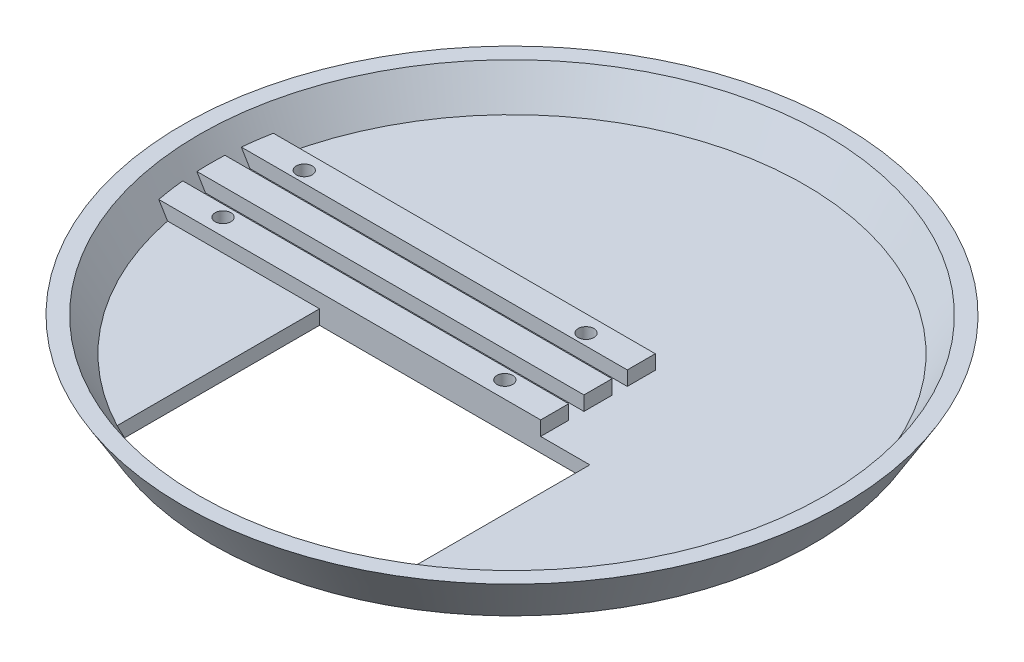
SolidWorks part; units mm, degrees
ref_plane "Front Plane" through (0, 0, 0) normal (0, 0, 1) x (1, 0, 0)
ref_plane "Top Plane" through (0, 0, 0) normal (0, 1, 0) x (1, 0, 0)
ref_plane "Right Plane" through (0, 0, 0) normal (1, 0, 0) x (0, 0, -1)
sketch "Sketch1" plane through (0, 0, 0) normal (0, 0, 1) x (1, 0, 0)
  line L0 (0, 0) -> (63, 0)
  line L1 (63, 0) -> (69, 10)
  line L6 (0, 3) -> (61.3014, 3)
  line L7 (61.3014, 3) -> (65.5014, 10)
  line L8 (69, 10) -> (65.5014, 10)
  line L9 (0, 0) -> (0, 3)
  line L10 (61.3014, 3) -> (66.4275, 11.5435) construction
  dimension "D1" = 69
  dimension "D2" = 63
  dimension "D3" = 10
  dimension "D4" = 3
revolve "Revolve1" add sketch "Sketch1" angle 360 about L9
sketch "Sketch2" plane through (0, 3, 0) normal (0, 1, 0) x (1, 0, 0)
  line L0 (-28.3, -12) -> (-28.3, -54.3781)
  line L1 (-28.3, -12) -> (28.3, -12)
  line L5 (28.3, -12) -> (28.3, -54.3781)
  arc A0 (-28.3, -54.3781) -> (28.3, -54.3781) centre (0, 0) ccw
  circle A3 centre (0, 0) radius 61.3014 construction
  dimension "D2" = 28.3
  dimension "D1" = 56.6
  dimension "D4" = 12
extrude "Cut-Extrude1" cut sketch "Sketch2" against normal through all
sketch "Sketch4" plane through (0, 0, 0) normal (1, 0, 0) x (0, 0, -1)
  line L0 (-6.1333, 3) -> (-12, 3)
  line L5 (-12, 3) -> (-12, 6)
  line L6 (-12, 6) -> (-6.1333, 6)
  line L7 (-6.1333, 6) -> (-6.1333, 3)
  line L8 (-2.9333, 3) -> (2.9333, 3)
  line L9 (2.9333, 3) -> (2.9333, 6)
  line L10 (2.9333, 6) -> (-2.9333, 6)
  line L11 (-2.9333, 6) -> (-2.9333, 3)
  line L12 (12, 3) -> (6.1333, 3)
  line L13 (6.1333, 3) -> (6.1333, 6)
  line L14 (6.1333, 6) -> (12, 6)
  line L15 (12, 6) -> (12, 3)
  point P13 (0, 3)
  dimension "D1" = 12
  dimension "D2" = 3
  dimension "D3" = 3
  dimension "D4" = 3.2
  dimension "D5" = 3.2
  dimension "D6" = 12
extrude "Boss-Extrude1" add sketch "Sketch4" along normal blind 10 and the other way blind 63.5
sketch "Sketch5" plane through (0, 0, 0) normal (0, 1, 0) x (1, 0, 0)
  line L0 (10, 2.9333) -> (10, -2.9333) construction
  circle A0 centre (7, -8.5) radius 1.65
  circle A1 centre (7, 0) radius 1.65
  circle A2 centre (7, 8.5) radius 1.65
  circle A6 centre (-52, 8.5) radius 1.65
  circle A8 centre (-52, -8.5) radius 1.65
  circle A9 centre (-22.5, 0) radius 1.65 [skipped]
  circle A10 centre (-52, 0) radius 1.65 [skipped]
  circle A11 centre (-22.5, 8.5) radius 1.65 [skipped]
  circle A12 centre (-22.5, -8.5) radius 1.65 [skipped]
  dimension "D2" = 3.3
  dimension "D3" = 8.5
  dimension "D6" = 3
  dimension "D7" = 59
  dimension "D4" = 8.5
  dimension "D5" = 3
extrude "Cut-Extrude2" cut sketch "Sketch5" along normal through all contours A2 | A0 | A8 | A6
sketch "Sketch7" [suppressed] plane through (10, 0, 0) normal (1, 0, 0) x (0, 0, -1)
  line L0 (-12, 37.9) -> (-6.1333, 37.9) construction
  line L1 (-12, 3) -> (-6.1333, 3)
  line L2 (-12, 3) -> (-12, 43)
  line L3 (-12, 43) -> (12, 43)
  line L4 (12, 3) -> (12, 43)
  line L5 (-2.9333, 37.9) -> (2.9333, 37.9) construction
  line L6 (-6.1333, 37.9) -> (-2.9333, 37.9)
  line L7 (-6.1333, 37.9) -> (-6.1333, 40.9)
  line L8 (-6.1333, 40.9) -> (-2.9333, 40.9)
  line L9 (-2.9333, 37.9) -> (-2.9333, 40.9)
  line L10 (12, 37.9) -> (6.1333, 37.9) construction
  line L11 (2.9333, 3) -> (2.9333, 6)
  line L12 (2.9333, 37.9) -> (6.1333, 37.9)
  line L13 (2.9333, 37.9) -> (2.9333, 40.9)
  line L14 (2.9333, 40.9) -> (6.1333, 40.9)
  line L15 (6.1333, 37.9) -> (6.1333, 40.9)
  line L20 (2.9333, 6) -> (6.1333, 6)
  line L21 (6.1333, 6) -> (6.1333, 3)
  line L22 (-6.1333, 3) -> (-6.1333, 6)
  line L23 (-6.1333, 6) -> (-2.9333, 6)
  line L24 (-2.9333, 6) -> (-2.9333, 3)
  line L25 (6.1333, 3) -> (12, 3)
  line L26 (-2.9333, 3) -> (2.9333, 3)
  circle A0 centre (0, 23.5) radius 8.5
  point P18 (0, 3)
  dimension "D6" = 17
  dimension "D7" = 20.5
  dimension "D1" = 24
  dimension "D2" = 40
  dimension "D3" = 3.2
  dimension "D4" = 3
  dimension "D5" = 37.9
sketch "Sketch8" plane through (10, 0, 0) normal (1, 0, 0) x (0, 0, -1)
  line L1 (-12, 6) -> (-6.1333, 6)
  line L2 (-12, 6) -> (-12, 3)
  line L3 (-12, 3) -> (-6.1333, 3)
  line L4 (-6.1333, 6) -> (-6.1333, 3)
  line L5 (-2.9333, 6) -> (2.9333, 6)
  line L6 (-2.9333, 6) -> (-2.9333, 3)
  line L7 (-2.9333, 3) -> (2.9333, 3)
  line L8 (2.9333, 6) -> (2.9333, 3)
  line L9 (6.1333, 6) -> (12, 6)
  line L10 (6.1333, 6) -> (6.1333, 3)
  line L11 (6.1333, 3) -> (12, 3)
  line L12 (12, 6) -> (12, 3)
extrude "Boss-Extrude3" add sketch "Sketch8" along normal blind 8
